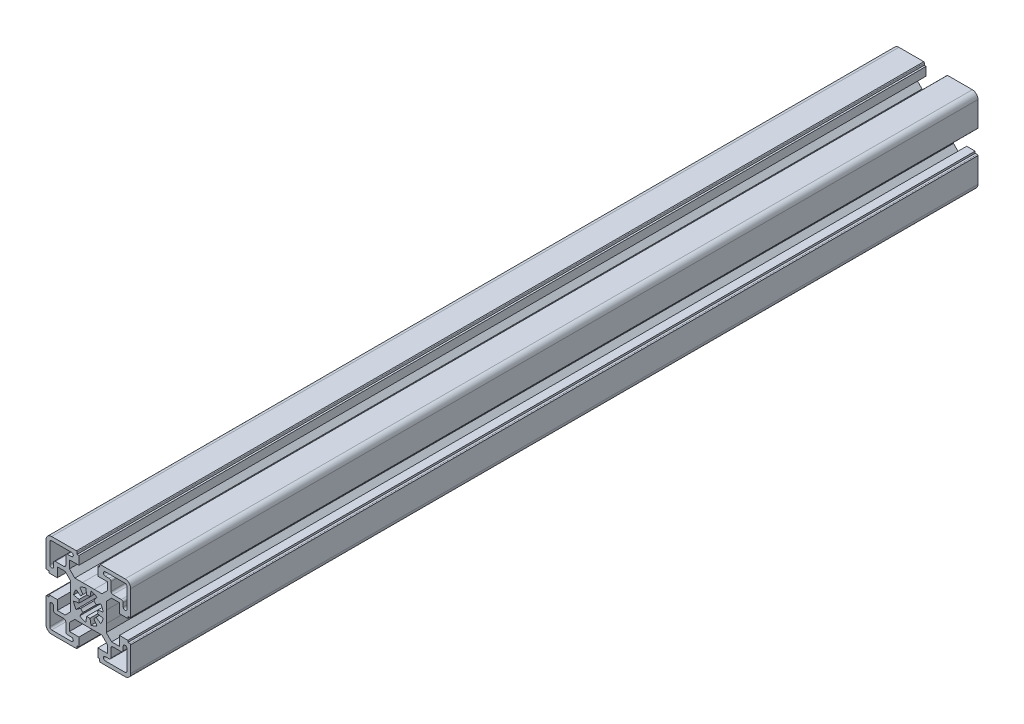
SolidWorks part; units mm, degrees
material "7050-T73510"
ref_plane "Front Plane" through (0, 0, 0) normal (0, 0, 1) x (1, 0, 0)
ref_plane "Top Plane" through (0, 0, 0) normal (0, 1, 0) x (1, 0, 0)
ref_plane "Right Plane" through (0, 0, 0) normal (1, 0, 0) x (0, 0, -1)
sketch "Sketch1" plane through (0, 0, 0) normal (0, 0, 1) x (1, 0, 0)
  line L0 (0, 34.901) -> (0, -38.8683) construction
  line L1 (-27.7848, -31.1091) -> (42.6814, -31.1091) construction
  line L3 (-0.8682, 4.924) -> (-1.3892, 7.8785)
  line L4 (-4.5886, 6.5532) -> (-2.8679, 4.0957)
  line L5 (-4.0957, 2.8679) -> (-6.5532, 4.5886)
  line L6 (-7.8784, 1.3892) -> (-4.924, 0.8682)
  line L10 (4.924, 0.8682) -> (7.8785, 1.3892)
  line L12 (6.5532, 4.5886) -> (4.0957, 2.8679)
  line L30 (-9.5, 3.1227) -> (-9.5, 7.207)
  line L31 (-9.5, 7.207) -> (-12.3429, 10.0499)
  line L32 (-12.3429, 10.0499) -> (-16.5, 10.0499)
  line L33 (-16.5, 10.0499) -> (-16.5, 4.9999)
  line L34 (-16.5, 4.9999) -> (-20.9999, 4.9999)
  line L35 (-20.9999, 4.9999) -> (-20.9999, 6)
  line L36 (-20.9999, 6) -> (-21.9999, 6)
  line L37 (-22.4999, 6.2999) -> (-22.4999, 19.5)
  line L38 (-19.4999, 22.5) -> (-6.3, 22.5)
  line L39 (-6, 21.9999) -> (-6, 20.9999)
  line L40 (-6, 20.9999) -> (-5, 20.9999)
  line L41 (-5, 20.9999) -> (-5, 16.5)
  line L42 (-5, 16.5) -> (-10.0501, 16.5)
  line L43 (-10.0501, 16.5) -> (-10.0501, 12.3428)
  line L44 (-10.0501, 12.3428) -> (-7.2071, 9.4999)
  line L45 (-7.2071, 9.4999) -> (-3.1228, 9.4999)
  line L82 (2.8679, 4.0957) -> (4.5886, 6.5532)
  line L83 (1.3892, 7.8784) -> (0.8682, 4.924)
  line L85 (3.1227, 9.5) -> (7.207, 9.5)
  line L86 (7.207, 9.5) -> (10.0499, 12.3429)
  line L87 (10.0499, 12.3429) -> (10.0499, 16.5)
  line L94 (-17.5001, 12) -> (-13.0001, 12)
  line L95 (-12.0001, 13) -> (-12.0001, 17.4999)
  line L96 (-11.0001, 18.4999) -> (-9.0001, 18.4999)
  line L97 (-19.5001, 20.5) -> (-9.0001, 20.5)
  line L98 (-20.5001, 8.9999) -> (-20.5001, 19.5)
  line L99 (-18.5001, 8.9999) -> (-18.5001, 11)
  line L101 (10.0499, 16.5) -> (4.9999, 16.5)
  line L102 (4.9999, 16.5) -> (4.9999, 20.9999)
  line L103 (4.9999, 20.9999) -> (6, 20.9999)
  line L104 (6, 20.9999) -> (6, 21.9999)
  line L105 (6.2999, 22.4999) -> (19.5, 22.4999)
  line L110 (22.5, 19.4999) -> (22.5, 6.3)
  line L111 (21.9999, 6) -> (20.9999, 6)
  line L118 (-3.1228, 9.4999) -> (3.1227, 9.5)
  line L119 (20.9999, 6) -> (20.9999, 5)
  line L124 (20.9999, 5) -> (16.5, 5)
  line L125 (16.5, 5) -> (16.5, 10.0501)
  line L126 (16.5, 10.0501) -> (12.3428, 10.0501)
  line L127 (12.3428, 10.0501) -> (9.4999, 7.2071)
  line L128 (9.4999, 7.2071) -> (9.4999, 3.1228)
  line L129 (12, 17.5001) -> (12, 13.0001)
  line L130 (13, 12.0001) -> (17.4999, 12.0001)
  line L131 (18.4999, 11.0001) -> (18.4999, 9.0001)
  line L132 (20.5, 19.5001) -> (20.5, 9.0001)
  line L133 (8.9999, 20.5001) -> (19.5, 20.5001)
  line L134 (8.9999, 18.5001) -> (11, 18.5001)
  line L135 (-9.5, 3.1227) -> (-9.4999, -3.1228)
  line L136 (9.4999, 3.1228) -> (9.5, -3.1227)
  line L137 (3.1228, -9.4999) -> (-3.1227, -9.5)
  line L138 (-0.8682, 4.924) -> (-1.3892, 7.8785)
  line L147 (0.8682, -4.924) -> (1.3892, -7.8785)
  line L148 (4.5886, -6.5532) -> (2.8679, -4.0957)
  line L149 (-4.924, -0.8682) -> (-7.8785, -1.3892)
  line L154 (4.0957, -2.8679) -> (6.5532, -4.5886)
  line L155 (7.8784, -1.3892) -> (4.924, -0.8682)
  line L157 (9.5, -3.1227) -> (9.5, -7.207)
  line L158 (9.5, -7.207) -> (12.3429, -10.0499)
  line L159 (12.3429, -10.0499) -> (16.5, -10.0499)
  line L160 (16.5, -10.0499) -> (16.5, -4.9999)
  line L161 (16.5, -4.9999) -> (20.9999, -4.9999)
  line L162 (20.9999, -4.9999) -> (20.9999, -6)
  line L163 (20.9999, -6) -> (21.9999, -6)
  line L164 (22.4999, -6.2999) -> (22.4999, -19.5)
  line L165 (19.4999, -22.5) -> (6.3, -22.5)
  line L166 (6, -21.9999) -> (6, -20.9999)
  line L167 (6, -20.9999) -> (5, -20.9999)
  line L168 (5, -20.9999) -> (5, -16.5)
  line L169 (5, -16.5) -> (10.0501, -16.5)
  line L176 (10.0501, -16.5) -> (10.0501, -12.3428)
  line L178 (4.924, 0.8682) -> (7.8785, 1.3892) [skipped]
  line L179 (6.5532, 4.5886) -> (4.0957, 2.8679) [skipped]
  line L180 (2.8679, 4.0957) -> (4.5886, 6.5532) [skipped]
  line L181 (1.3892, 7.8784) -> (0.8682, 4.924) [skipped]
  line L183 (3.1227, 9.5) -> (7.207, 9.5) [skipped]
  line L184 (7.207, 9.5) -> (10.0499, 12.3429) [skipped]
  line L185 (10.0499, 12.3429) -> (10.0499, 16.5) [skipped]
  line L186 (10.0499, 16.5) -> (4.9999, 16.5) [skipped]
  line L187 (4.9999, 16.5) -> (4.9999, 20.9999) [skipped]
  line L188 (4.9999, 20.9999) -> (6, 20.9999) [skipped]
  line L189 (6, 20.9999) -> (6, 21.9999) [skipped]
  line L190 (6.2999, 22.4999) -> (19.5, 22.4999) [skipped]
  line L191 (22.5, 19.4999) -> (22.5, 6.3) [skipped]
  line L192 (21.9999, 6) -> (20.9999, 6) [skipped]
  line L193 (20.9999, 6) -> (20.9999, 5) [skipped]
  line L194 (20.9999, 5) -> (16.5, 5) [skipped]
  line L195 (16.5, 5) -> (16.5, 10.0501) [skipped]
  line L196 (16.5, 10.0501) -> (12.3428, 10.0501) [skipped]
  line L197 (12.3428, 10.0501) -> (9.4999, 7.2071) [skipped]
  line L198 (9.4999, 7.2071) -> (9.4999, 3.1228) [skipped]
  line L199 (12, 17.5001) -> (12, 13.0001) [skipped]
  line L200 (13, 12.0001) -> (17.4999, 12.0001) [skipped]
  line L201 (18.4999, 11.0001) -> (18.4999, 9.0001) [skipped]
  line L202 (20.5, 19.5001) -> (20.5, 9.0001) [skipped]
  line L203 (8.9999, 20.5001) -> (19.5, 20.5001) [skipped]
  line L204 (8.9999, 18.5001) -> (11, 18.5001) [skipped]
  line L206 (0.8682, -4.924) -> (1.3892, -7.8785) [skipped]
  line L207 (4.5886, -6.5532) -> (2.8679, -4.0957) [skipped]
  line L208 (4.0957, -2.8679) -> (6.5532, -4.5886) [skipped]
  line L209 (7.8784, -1.3892) -> (4.924, -0.8682) [skipped]
  line L210 (9.5, -3.1227) -> (9.5, -7.207) [skipped]
  line L211 (9.5, -7.207) -> (12.3429, -10.0499) [skipped]
  line L212 (12.3429, -10.0499) -> (16.5, -10.0499) [skipped]
  line L213 (16.5, -10.0499) -> (16.5, -4.9999) [skipped]
  line L214 (16.5, -4.9999) -> (20.9999, -4.9999) [skipped]
  line L215 (20.9999, -4.9999) -> (20.9999, -6) [skipped]
  line L216 (20.9999, -6) -> (21.9999, -6) [skipped]
  line L217 (22.4999, -6.2999) -> (22.4999, -19.5) [skipped]
  line L218 (19.4999, -22.5) -> (6.3, -22.5) [skipped]
  line L219 (6, -21.9999) -> (6, -20.9999) [skipped]
  line L220 (6, -20.9999) -> (5, -20.9999) [skipped]
  line L221 (5, -20.9999) -> (5, -16.5) [skipped]
  line L222 (5, -16.5) -> (10.0501, -16.5) [skipped]
  line L223 (10.0501, -16.5) -> (10.0501, -12.3428) [skipped]
  line L224 (10.0501, -12.3428) -> (7.2071, -9.4999) [skipped]
  line L225 (7.2071, -9.4999) -> (3.1228, -9.4999) [skipped]
  line L226 (17.5001, -12) -> (13.0001, -12) [skipped]
  line L227 (12.0001, -13) -> (12.0001, -17.4999) [skipped]
  line L228 (11.0001, -18.4999) -> (9.0001, -18.4999) [skipped]
  line L229 (19.5001, -20.5) -> (9.0001, -20.5) [skipped]
  line L230 (20.5001, -8.9999) -> (20.5001, -19.5) [skipped]
  line L231 (18.5001, -8.9999) -> (18.5001, -11) [skipped]
  line L235 (-6.5532, -4.5886) -> (-4.0957, -2.8679) [skipped]
  line L236 (-2.8679, -4.0957) -> (-4.5886, -6.5532) [skipped]
  line L237 (-1.3892, -7.8784) -> (-0.8682, -4.924) [skipped]
  line L238 (-3.1227, -9.5) -> (-7.207, -9.5) [skipped]
  line L239 (-7.207, -9.5) -> (-10.0499, -12.3429) [skipped]
  line L240 (-10.0499, -12.3429) -> (-10.0499, -16.5) [skipped]
  line L241 (-10.0499, -16.5) -> (-4.9999, -16.5) [skipped]
  line L242 (-4.9999, -16.5) -> (-4.9999, -20.9999) [skipped]
  line L243 (-4.9999, -20.9999) -> (-6, -20.9999) [skipped]
  line L244 (-6, -20.9999) -> (-6, -21.9999) [skipped]
  line L245 (-6.2999, -22.4999) -> (-19.5, -22.4999) [skipped]
  line L246 (-22.5, -19.4999) -> (-22.5, -6.3) [skipped]
  line L247 (-21.9999, -6) -> (-20.9999, -6) [skipped]
  line L248 (-20.9999, -6) -> (-20.9999, -5) [skipped]
  line L249 (-20.9999, -5) -> (-16.5, -5) [skipped]
  line L250 (-16.5, -5) -> (-16.5, -10.0501) [skipped]
  line L251 (-16.5, -10.0501) -> (-12.3428, -10.0501) [skipped]
  line L252 (-12.3428, -10.0501) -> (-9.4999, -7.2071) [skipped]
  line L253 (-9.4999, -7.2071) -> (-9.4999, -3.1228) [skipped]
  line L254 (-12, -17.5001) -> (-12, -13.0001) [skipped]
  line L255 (-13, -12.0001) -> (-17.4999, -12.0001) [skipped]
  line L256 (-18.4999, -11.0001) -> (-18.4999, -9.0001) [skipped]
  line L257 (-20.5, -19.5001) -> (-20.5, -9.0001) [skipped]
  line L258 (-8.9999, -20.5001) -> (-19.5, -20.5001) [skipped]
  line L259 (-8.9999, -18.5001) -> (-11, -18.5001) [skipped]
  line L261 (10.0501, -12.3428) -> (7.2071, -9.4999)
  line L262 (7.2071, -9.4999) -> (3.1228, -9.4999)
  line L263 (17.5001, -12) -> (13.0001, -12)
  line L264 (12.0001, -13) -> (12.0001, -17.4999)
  line L265 (11.0001, -18.4999) -> (9.0001, -18.4999)
  line L266 (19.5001, -20.5) -> (9.0001, -20.5)
  line L267 (20.5001, -8.9999) -> (20.5001, -19.5)
  line L268 (18.5001, -8.9999) -> (18.5001, -11)
  line L272 (4.924, 0.8682) -> (7.8785, 1.3892)
  line L275 (-4.924, -0.8682) -> (-7.8785, -1.3892)
  line L276 (-6.5532, -4.5886) -> (-4.0957, -2.8679)
  line L277 (-2.8679, -4.0957) -> (-4.5886, -6.5532)
  line L278 (-1.3892, -7.8784) -> (-0.8682, -4.924)
  line L280 (-3.1227, -9.5) -> (-7.207, -9.5)
  line L281 (-7.207, -9.5) -> (-10.0499, -12.3429)
  line L282 (-10.0499, -12.3429) -> (-10.0499, -16.5)
  line L283 (-10.0499, -16.5) -> (-4.9999, -16.5)
  line L284 (-4.9999, -16.5) -> (-4.9999, -20.9999)
  line L285 (-4.9999, -20.9999) -> (-6, -20.9999)
  line L286 (-6, -20.9999) -> (-6, -21.9999)
  line L287 (-6.2999, -22.4999) -> (-19.5, -22.4999)
  line L288 (-22.5, -19.4999) -> (-22.5, -6.3)
  line L289 (-21.9999, -6) -> (-20.9999, -6)
  line L290 (-20.9999, -6) -> (-20.9999, -5)
  line L291 (-20.9999, -5) -> (-16.5, -5)
  line L292 (-16.5, -5) -> (-16.5, -10.0501)
  line L293 (-16.5, -10.0501) -> (-12.3428, -10.0501)
  line L294 (-12.3428, -10.0501) -> (-9.4999, -7.2071)
  line L295 (-9.4999, -7.2071) -> (-9.4999, -3.1228)
  line L296 (-12, -17.5001) -> (-12, -13.0001)
  line L297 (-13, -12.0001) -> (-17.4999, -12.0001)
  line L298 (-18.4999, -11.0001) -> (-18.4999, -9.0001)
  line L299 (-20.5, -19.5001) -> (-20.5, -9.0001)
  line L300 (-8.9999, -20.5001) -> (-19.5, -20.5001)
  line L301 (-8.9999, -18.5001) -> (-11, -18.5001)
  line L305 (0.8682, -4.924) -> (1.3892, -7.8785)
  arc A1 (-1.3892, 7.8785) -> (-4.5886, 6.5532) centre (0, 0) ccw
  arc A2 (-2.8679, 4.0957) -> (-4.0957, 2.8679) centre (0, 0) ccw
  arc A3 (-6.5532, 4.5886) -> (-7.8784, 1.3892) centre (0, 0) ccw
  arc A4 (-4.924, 0.8682) -> (-4.924, -0.8682) centre (0, 0) ccw
  arc A7 (0.8682, 4.924) -> (-0.8682, 4.924) centre (0, 0) ccw
  arc A8 (7.8785, 1.3892) -> (6.5532, 4.5886) centre (0, 0) ccw
  arc A20 (-22.4999, 6.2999) -> (-21.9999, 6) centre (-22.041, 6.4983) ccw
  arc A21 (-19.4999, 22.5) -> (-22.4999, 19.5) centre (-19.4999, 19.5) ccw
  arc A22 (-6, 21.9999) -> (-6.3, 22.5) centre (-6.4984, 22.041) ccw
  arc A32 (4.0957, 2.8679) -> (2.8679, 4.0957) centre (0, 0) ccw
  arc A33 (4.5886, 6.5532) -> (1.3892, 7.8784) centre (0, 0) ccw
  arc A44 (-17.5001, 12) -> (-18.5001, 11) centre (-17.5001, 11) ccw
  arc A45 (-13.0001, 12) -> (-12.0001, 13) centre (-13.0001, 13) ccw
  arc A46 (-11.0001, 18.4999) -> (-12.0001, 17.4999) centre (-11.0001, 17.4999) ccw
  arc A47 (-9.0001, 18.4999) -> (-9.0001, 20.5) centre (-9.0001, 19.5) ccw
  arc A48 (-19.5001, 20.5) -> (-20.5001, 19.5) centre (-19.5001, 19.5) ccw
  arc A49 (-20.5001, 8.9999) -> (-18.5001, 8.9999) centre (-19.5001, 8.9999) ccw
  arc A51 (0.8682, 4.924) -> (-0.8682, 4.924) centre (0, 0) ccw
  arc A52 (4.924, -0.8682) -> (4.924, 0.8682) centre (0, 0) ccw
  arc A53 (6.2999, 22.4999) -> (6, 21.9999) centre (6.4983, 22.041) ccw
  arc A60 (-7.8785, -1.3892) -> (-6.5532, -4.5886) centre (0, 0) ccw
  arc A64 (22.5, 19.4999) -> (19.5, 22.4999) centre (19.5, 19.4999) ccw
  arc A65 (21.9999, 6) -> (22.5, 6.3) centre (22.041, 6.4984) ccw
  arc A66 (12, 17.5001) -> (11, 18.5001) centre (11, 17.5001) ccw
  arc A73 (7.8785, 1.3892) -> (6.5532, 4.5886) centre (0, 0) ccw [skipped]
  arc A74 (4.0957, 2.8679) -> (2.8679, 4.0957) centre (0, 0) ccw [skipped]
  arc A75 (4.5886, 6.5532) -> (1.3892, 7.8784) centre (0, 0) ccw [skipped]
  arc A76 (6.2999, 22.4999) -> (6, 21.9999) centre (6.4983, 22.041) ccw [skipped]
  arc A77 (22.5, 19.4999) -> (19.5, 22.4999) centre (19.5, 19.4999) ccw [skipped]
  arc A78 (21.9999, 6) -> (22.5, 6.3) centre (22.041, 6.4984) ccw [skipped]
  arc A79 (12, 17.5001) -> (11, 18.5001) centre (11, 17.5001) ccw [skipped]
  arc A80 (12, 13.0001) -> (13, 12.0001) centre (13, 13.0001) ccw [skipped]
  arc A81 (18.4999, 11.0001) -> (17.4999, 12.0001) centre (17.4999, 11.0001) ccw [skipped]
  arc A82 (18.4999, 9.0001) -> (20.5, 9.0001) centre (19.5, 9.0001) ccw [skipped]
  arc A83 (20.5, 19.5001) -> (19.5, 20.5001) centre (19.5, 19.5001) ccw [skipped]
  arc A84 (8.9999, 20.5001) -> (8.9999, 18.5001) centre (8.9999, 19.5001) ccw [skipped]
  arc A85 (1.3892, -7.8785) -> (4.5886, -6.5532) centre (0, 0) ccw [skipped]
  arc A86 (2.8679, -4.0957) -> (4.0957, -2.8679) centre (0, 0) ccw [skipped]
  arc A87 (6.5532, -4.5886) -> (7.8784, -1.3892) centre (0, 0) ccw [skipped]
  arc A88 (4.924, -0.8682) -> (4.924, 0.8682) centre (0, 0) ccw [skipped]
  arc A89 (22.4999, -6.2999) -> (21.9999, -6) centre (22.041, -6.4983) ccw [skipped]
  arc A90 (19.4999, -22.5) -> (22.4999, -19.5) centre (19.4999, -19.5) ccw [skipped]
  arc A91 (6, -21.9999) -> (6.3, -22.5) centre (6.4984, -22.041) ccw [skipped]
  arc A92 (17.5001, -12) -> (18.5001, -11) centre (17.5001, -11) ccw [skipped]
  arc A93 (13.0001, -12) -> (12.0001, -13) centre (13.0001, -13) ccw [skipped]
  arc A94 (11.0001, -18.4999) -> (12.0001, -17.4999) centre (11.0001, -17.4999) ccw [skipped]
  arc A95 (9.0001, -18.4999) -> (9.0001, -20.5) centre (9.0001, -19.5) ccw [skipped]
  arc A96 (19.5001, -20.5) -> (20.5001, -19.5) centre (19.5001, -19.5) ccw [skipped]
  arc A97 (20.5001, -8.9999) -> (18.5001, -8.9999) centre (19.5001, -8.9999) ccw [skipped]
  arc A98 (-4.0957, -2.8679) -> (-2.8679, -4.0957) centre (0, 0) ccw [skipped]
  arc A99 (-4.5886, -6.5532) -> (-1.3892, -7.8784) centre (0, 0) ccw [skipped]
  arc A100 (-0.8682, -4.924) -> (0.8682, -4.924) centre (0, 0) ccw [skipped]
  arc A101 (-6.2999, -22.4999) -> (-6, -21.9999) centre (-6.4983, -22.041) ccw [skipped]
  arc A102 (-22.5, -19.4999) -> (-19.5, -22.4999) centre (-19.5, -19.4999) ccw [skipped]
  arc A103 (-21.9999, -6) -> (-22.5, -6.3) centre (-22.041, -6.4984) ccw [skipped]
  arc A104 (-12, -17.5001) -> (-11, -18.5001) centre (-11, -17.5001) ccw [skipped]
  arc A105 (-12, -13.0001) -> (-13, -12.0001) centre (-13, -13.0001) ccw [skipped]
  arc A106 (-18.4999, -11.0001) -> (-17.4999, -12.0001) centre (-17.4999, -11.0001) ccw [skipped]
  arc A107 (-18.4999, -9.0001) -> (-20.5, -9.0001) centre (-19.5, -9.0001) ccw [skipped]
  arc A108 (-20.5, -19.5001) -> (-19.5, -20.5001) centre (-19.5, -19.5001) ccw [skipped]
  arc A109 (-8.9999, -20.5001) -> (-8.9999, -18.5001) centre (-8.9999, -19.5001) ccw [skipped]
  arc A110 (12, 13.0001) -> (13, 12.0001) centre (13, 13.0001) ccw
  arc A111 (18.4999, 11.0001) -> (17.4999, 12.0001) centre (17.4999, 11.0001) ccw
  arc A112 (18.4999, 9.0001) -> (20.5, 9.0001) centre (19.5, 9.0001) ccw
  arc A113 (20.5, 19.5001) -> (19.5, 20.5001) centre (19.5, 19.5001) ccw
  arc A114 (8.9999, 20.5001) -> (8.9999, 18.5001) centre (8.9999, 19.5001) ccw
  arc A115 (-1.3892, 7.8785) -> (-4.5886, 6.5532) centre (0, 0) ccw
  arc A116 (1.3892, -7.8785) -> (4.5886, -6.5532) centre (0, 0) ccw
  arc A117 (2.8679, -4.0957) -> (4.0957, -2.8679) centre (0, 0) ccw
  arc A118 (6.5532, -4.5886) -> (7.8784, -1.3892) centre (0, 0) ccw
  arc A119 (4.924, -0.8682) -> (4.924, 0.8682) centre (0, 0) ccw
  arc A120 (-0.8682, -4.924) -> (0.8682, -4.924) centre (0, 0) ccw
  arc A121 (22.4999, -6.2999) -> (21.9999, -6) centre (22.041, -6.4983) ccw
  arc A122 (19.4999, -22.5) -> (22.4999, -19.5) centre (19.4999, -19.5) ccw
  arc A123 (6, -21.9999) -> (6.3, -22.5) centre (6.4984, -22.041) ccw
  arc A124 (17.5001, -12) -> (18.5001, -11) centre (17.5001, -11) ccw
  arc A125 (13.0001, -12) -> (12.0001, -13) centre (13.0001, -13) ccw
  arc A126 (11.0001, -18.4999) -> (12.0001, -17.4999) centre (11.0001, -17.4999) ccw
  arc A127 (9.0001, -18.4999) -> (9.0001, -20.5) centre (9.0001, -19.5) ccw
  arc A128 (19.5001, -20.5) -> (20.5001, -19.5) centre (19.5001, -19.5) ccw
  arc A129 (20.5001, -8.9999) -> (18.5001, -8.9999) centre (19.5001, -8.9999) ccw
  arc A130 (7.8785, 1.3892) -> (6.5532, 4.5886) centre (0, 0) ccw
  arc A131 (-7.8785, -1.3892) -> (-6.5532, -4.5886) centre (0, 0) ccw
  arc A132 (-4.0957, -2.8679) -> (-2.8679, -4.0957) centre (0, 0) ccw
  arc A133 (-4.5886, -6.5532) -> (-1.3892, -7.8784) centre (0, 0) ccw
  arc A134 (-0.8682, -4.924) -> (0.8682, -4.924) centre (0, 0) ccw
  arc A135 (-4.924, 0.8682) -> (-4.924, -0.8682) centre (0, 0) ccw
  arc A136 (-6.2999, -22.4999) -> (-6, -21.9999) centre (-6.4983, -22.041) ccw
  arc A137 (-22.5, -19.4999) -> (-19.5, -22.4999) centre (-19.5, -19.4999) ccw
  arc A138 (-21.9999, -6) -> (-22.5, -6.3) centre (-22.041, -6.4984) ccw
  arc A139 (-12, -17.5001) -> (-11, -18.5001) centre (-11, -17.5001) ccw
  arc A140 (-12, -13.0001) -> (-13, -12.0001) centre (-13, -13.0001) ccw
  arc A141 (-18.4999, -11.0001) -> (-17.4999, -12.0001) centre (-17.4999, -11.0001) ccw
  arc A142 (-18.4999, -9.0001) -> (-20.5, -9.0001) centre (-19.5, -9.0001) ccw
  arc A143 (-20.5, -19.5001) -> (-19.5, -20.5001) centre (-19.5, -19.5001) ccw
  arc A144 (-8.9999, -20.5001) -> (-8.9999, -18.5001) centre (-8.9999, -19.5001) ccw
  arc A145 (1.3892, -7.8785) -> (4.5886, -6.5532) centre (0, 0) ccw
  point P528 (0, 0)
  dimension "D1" = 4
  dimension "D2" = 4
extrude "Boss-Extrude1" add sketch "Sketch1" along normal blind 450
